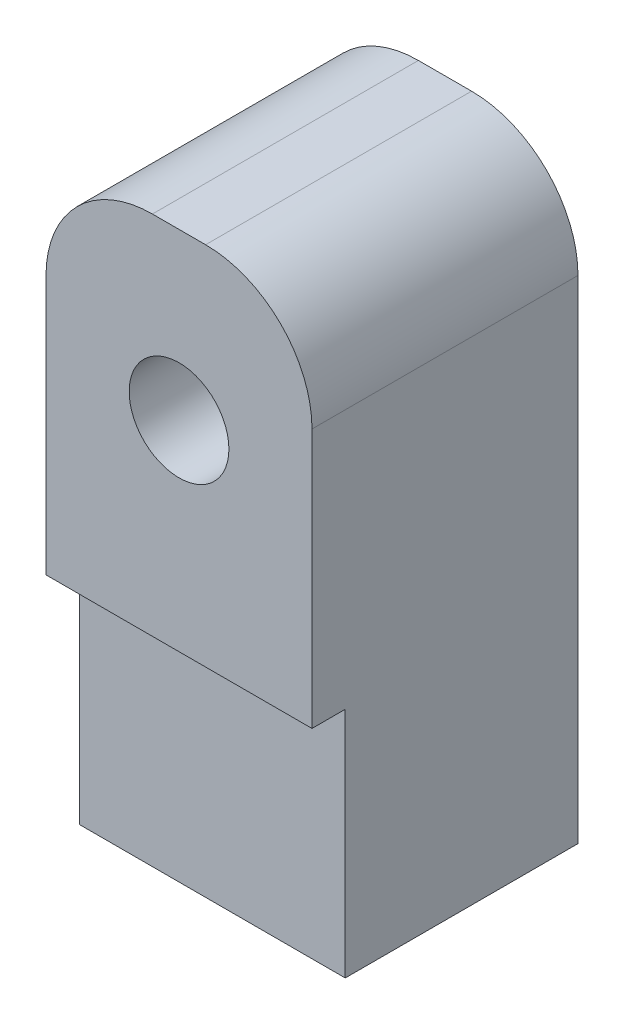
SolidWorks part; units mm, degrees
ref_plane "Front Plane" through (0, 0, 0) normal (0, 0, 1) x (1, 0, 0)
ref_plane "Top Plane" through (0, 0, 0) normal (0, 1, 0) x (1, 0, 0)
ref_plane "Right Plane" through (0, 0, 0) normal (1, 0, 0) x (0, 0, -1)
sketch "Sketch1" plane through (0, 0, 0) normal (0, 1, 0) x (1, 0, 0)
  line L1 (-12.7, -12.7) -> (12.7, -12.7)
  line L2 (-12.7, -12.7) -> (-12.7, 12.7)
  line L3 (-12.7, 12.7) -> (12.7, 12.7)
  line L4 (12.7, -12.7) -> (12.7, 12.7)
  point P0 (0, 0)
  dimension "D1" = 25.4
  dimension "D2" = 25.4
extrude "Boss-Extrude1" add sketch "Sketch1" along normal blind 57.15
sketch "Sketch2" plane through (0, 0, 0) normal (0, -1, 0) x (1, 0, 0)
  line L1 (-12.7, -12.7) -> (-12.7, 12.7) construction
  line L2 (-12.7, 9.525) -> (12.7, 9.525)
  line L3 (12.7, 12.7) -> (12.7, -12.7) construction
  line L4 (12.7, 9.525) -> (12.7, 12.7)
  line L5 (-12.7, 12.7) -> (12.7, 12.7) construction
  line L6 (12.7, 12.7) -> (-12.7, 12.7)
  line L7 (-12.7, 12.7) -> (-12.7, 9.525)
extrude "Cut-Extrude1" cut sketch "Sketch2" against normal blind 22.225
sketch "Sketch3" plane through (0, 0, 12.7) normal (0, 0, 1) x (1, 0, 0)
  circle A0 centre (0.0021, 41.3626) radius 4.7625
extrude "Cut-Extrude4" cut sketch "Sketch3" against normal blind 25.4 contours A0
sketch "Sketch4" plane through (0, 0, -12.7) normal (0, 0, -1) x (-1, 0, 0)
  circle A0 centre (-0.0021, 41.3626) radius 6.0325
extrude "Cut-Extrude5" cut sketch "Sketch4" against normal blind 3.175
sketch "Sketch5" plane through (0, 0, 0) normal (0, -1, 0) x (1, 0, 0)
  circle A0 centre (0, 0) radius 6.35
extrude "Cut-Extrude6" cut sketch "Sketch5" against normal blind 30.1752
fillet "Fillet1" radius 10.16 2 edges at (-12.7, 57.15, 0) (12.7, 57.15, 0)
